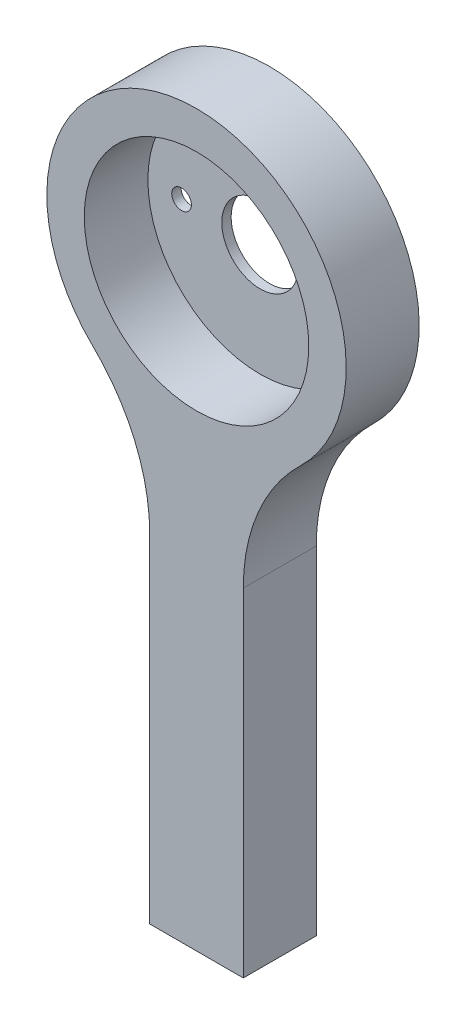
SolidWorks part; units mm, degrees
material "Nylon 101"
ref_plane "Front Plane" through (0, 0, 0) normal (0, 0, 1) x (1, 0, 0)
ref_plane "Top Plane" through (0, 0, 0) normal (0, 1, 0) x (1, 0, 0)
ref_plane "Right Plane" through (0, 0, 0) normal (1, 0, 0) x (0, 0, -1)
sketch "Sketch1" plane through (0, 0, 0) normal (0, 0, 1) x (1, 0, 0)
  line L0 (-2.5, -31) -> (2.5, -31)
  line L2 (-2.5, -12.9518) -> (-2.5, -31)
  line L4 (2.5, -12.9518) -> (2.5, -31)
  circle A0 centre (0, 0) radius 6
  arc A1 (5.5556, -5.7564) -> (-5.5556, -5.7564) centre (0, 0) ccw
  arc A2 (5.5556, -5.7564) -> (2.5, -12.9518) centre (12.5, -12.9518) ccw
  arc A3 (-5.5556, -5.7564) -> (-2.5, -12.9518) centre (-12.5, -12.9518) cw
  dimension "D1" = 12
  dimension "D2" = 2
  dimension "D5" = 10
  dimension "D4" = 31
  dimension "D3" = 5
extrude "Boss-Extrude1" add sketch "Sketch1" along normal blind 3.9
sketch "Sketch4" plane through (0, 0, 0) normal (0, 0, 1) x (1, 0, 0)
  line L0 (4.2, 0) -> (-4.2, 0) construction
  circle A0 centre (0, 0) radius 8
  circle A1 centre (0, 0) radius 6
  circle A2 centre (0, 0) radius 6 construction
  arc A3 (5.5556, -5.7564) -> (-5.5556, -5.7564) centre (0, 0) ccw construction
  circle A4 centre (4.2, 0) radius 0.525
  circle A5 centre (-4.2, 0) radius 0.525
  point P16 (0, 0)
  dimension "D1" = 1.05
  dimension "D2" = 8.4
sketch "Sketch5" plane through (0, 0, 0) normal (0, 0, -1) x (-1, 0, 0)
  circle A0 centre (0, 0) radius 2.05
  circle A1 centre (4.2, 0) radius 0.525
  circle A2 centre (4.2, 0) radius 0.525
  circle A3 centre (-4.2, 0) radius 0.525
  circle A4 centre (-4.2, 0) radius 0.525
  circle A7 centre (0, 0) radius 8
  circle A8 centre (0, 0) radius 8
  dimension "D3" = 4.1
  dimension "D1" = 0
  dimension "D2" = 0
  dimension "D4" = 0
extrude "Boss-Extrude3" add sketch "Sketch5" against normal blind 0.5
